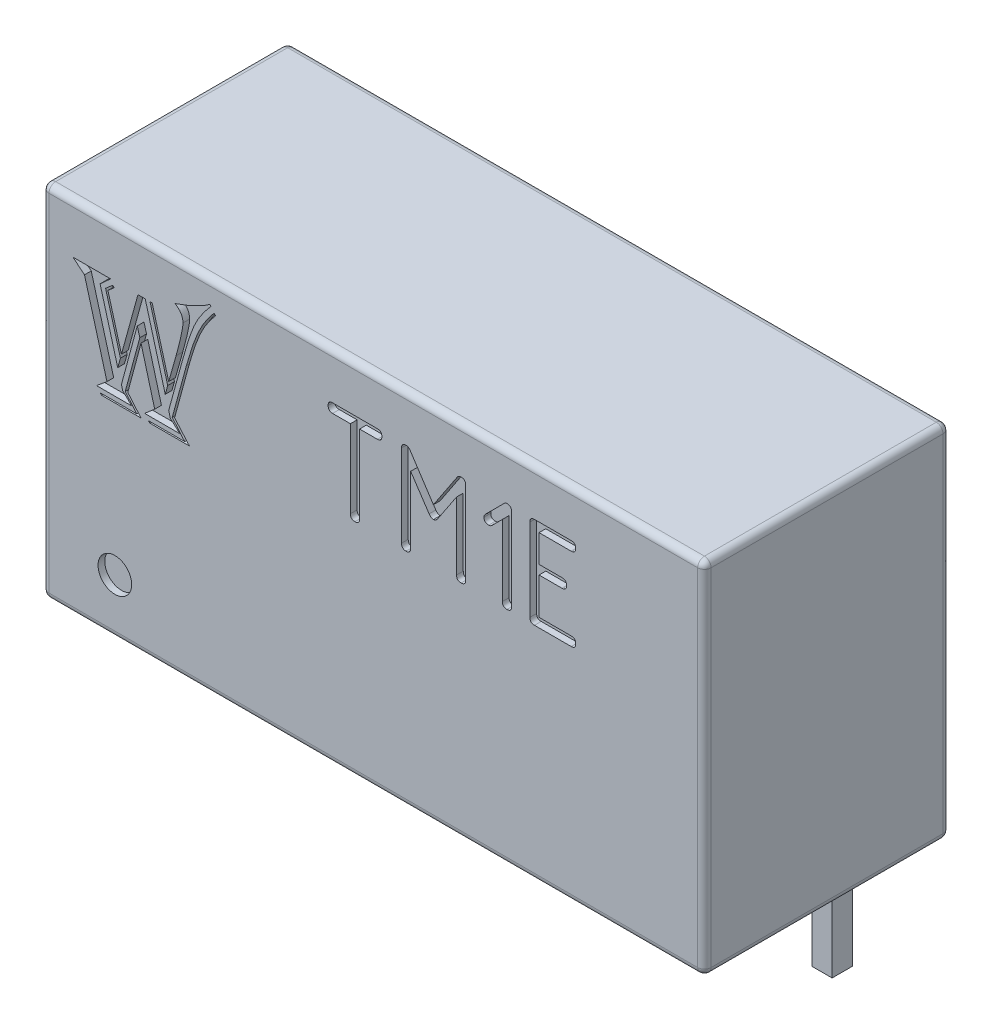
SolidWorks part; units mm, degrees
ref_plane "Front" through (0, 0, 0) normal (0, 0, 1) x (1, 0, 0)
ref_plane "Top" through (0, 0, 0) normal (0, 1, 0) x (1, 0, 0)
ref_plane "Right" through (0, 0, 0) normal (1, 0, 0) x (0, 0, -1)
sketch "Эскиз2" plane through (0, 0, 0) normal (0, 1, 0) x (1, 0, 0)
  line L1 (-9.85, 3.65) -> (9.85, 3.65)
  line L2 (-9.85, 3.65) -> (-9.85, -3.65)
  line L3 (-9.85, -3.65) -> (9.85, -3.65)
  line L4 (9.85, 3.65) -> (9.85, -3.65)
  line L5 (-9.85, 3.65) -> (9.85, -3.65) construction
  line L6 (-9.85, -3.65) -> (9.85, 3.65) construction
  point P0 (0, 0)
  dimension "D1" = 19.7
  dimension "D2" = 7.3
extrude "Бобышка-Вытянуть1" add sketch "Эскиз2" along normal blind 10.7
fillet "Скругление1" radius 0.2 12 edges at (9.85, 5.35, -3.65) (-9.85, 5.35, -3.65) (-9.85, 5.35, 3.65) (9.85, 5.35, 3.65) (0, 10.7, 3.65) (-9.85, 10.7, 0) (0, 10.7, -3.65) (9.85, 10.7, 0) (0, 0, -3.65) (-9.85, 0, 0) (0, 0, 3.65) (9.85, 0, 0)
sketch "Эскиз3" plane through (0, 0, 0) normal (0, -1, 0) x (1, 0, 0)
  line L0 (0, 5.1874) -> (0, -5.2849) construction
  line L1 (-12.0823, -2.38) -> (11.717, -2.38) construction
  line L2 (9.65, -3.65) -> (-9.65, -3.65) construction
  line L3 (-7.62, 5.164) -> (-7.62, -5.3084) construction
  line L4 (-7.92, -2.08) -> (-7.32, -2.08)
  line L5 (-7.92, -2.08) -> (-7.92, -2.68)
  line L6 (-7.92, -2.68) -> (-7.32, -2.68)
  line L7 (-7.32, -2.08) -> (-7.32, -2.68)
  line L8 (-7.92, -2.08) -> (-7.32, -2.68) construction
  line L9 (-7.92, -2.68) -> (-7.32, -2.08) construction
  point P7 (0.7026, -2.38)
  point P14 (-7.62, -2.38)
  point P18 (-7.62, -2.38)
  dimension "D1" = 1.27
  dimension "D2" = 0.6
  dimension "D3" = 0.6
  dimension "D4" = 7.62
extrude "Бобышка-Вытянуть2" add sketch "Эскиз3" along normal blind 4
chamfer "Фаска1" distance 0.2 angle 45 4 edges at (-7.62, -4, -2.68) (-7.92, -4, -2.38) (-7.62, -4, -2.08) (-7.32, -4, -2.38)
sketch "Эскиз4" plane through (0, 0, 3.65) normal (0, 0, 1) x (1, 0, 0)
  circle A0 centre (-7.6895, 1.6463) radius 0.5
  text T0 "TM1E\r\n" font "ГОСТ тип А" height in points 12
  text T1 "W" font "Algerian" height in points 10
  dimension "D1" = 1
extrude "Вырез-Вытянуть1" cut sketch "Эскиз4" against normal blind 0.2
pattern_linear "Линейный массив2" count 7 spacing 2.54 along (1, 0, 0) skipping (2, 0), (3, 0) of "Бобышка-Вытянуть2", "Фаска1"
